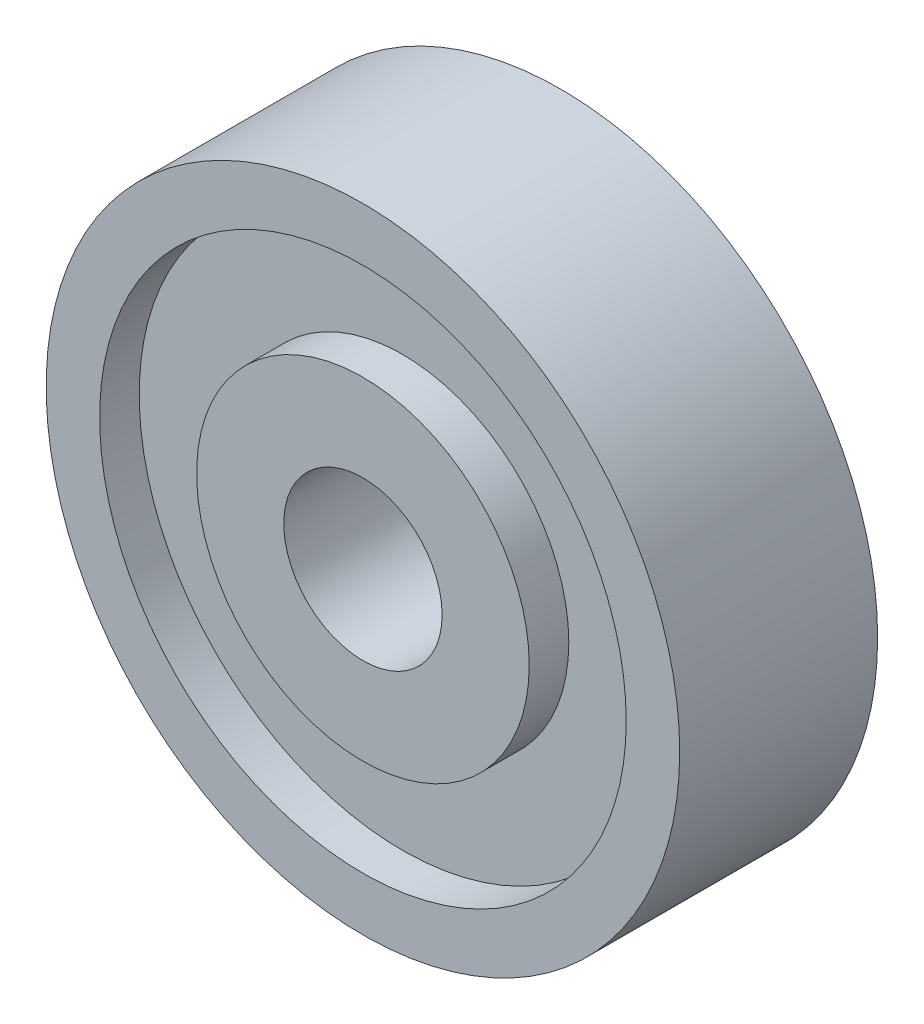
SolidWorks part; units mm, degrees
material "AISI 1020"
ref_plane "Front Plane" through (0, 0, 0) normal (0, 0, 1) x (1, 0, 0)
ref_plane "Top Plane" through (0, 0, 0) normal (0, 1, 0) x (1, 0, 0)
ref_plane "Right Plane" through (0, 0, 0) normal (1, 0, 0) x (0, 0, -1)
sketch "Sketch1" plane through (0, 0, 0) normal (0, 0, 1) x (1, 0, 0)
  circle A0 centre (0, 0) radius 8
  circle A1 centre (0, 0) radius 2
  dimension "D1" = 16
  dimension "D2" = 4
extrude "Extrude1" add sketch "Sketch1" along normal blind 5
sketch "Sketch2" plane through (0, 0, 5) normal (0, 0, 1) x (1, 0, 0)
  circle A0 centre (0, 0) radius 4.2
  circle A1 centre (0, 0) radius 6.65
  dimension "D1" = 8.4
  dimension "D2" = 13.3
extrude "Cut-Extrude1" cut sketch "Sketch2" against normal blind 1
ref_plane "Plane1" through (0, 0, 2.5) normal (0, 0, -1) x (-1, 0, 0)
mirror "Mirror1" about plane through (0, 0, 2.5) normal (0, 0, -1) of "Cut-Extrude1"
